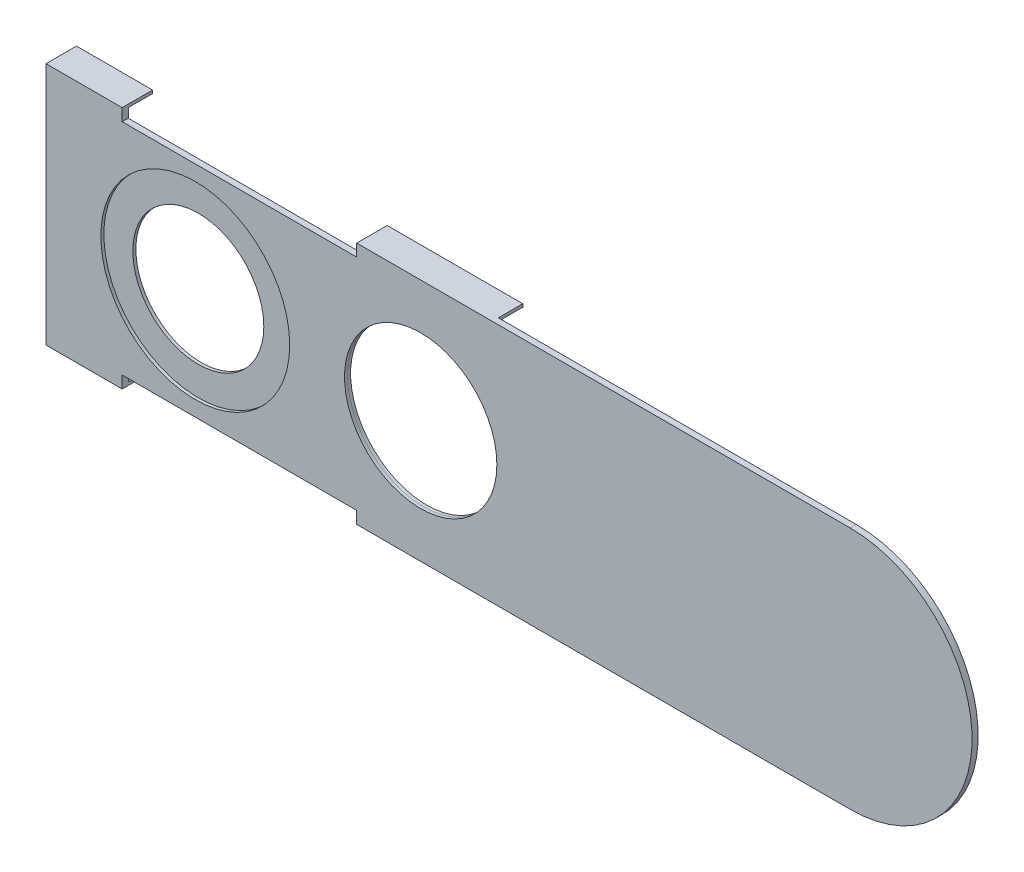
SolidWorks part; units mm, degrees
material "Nickel"
ref_plane "Front Plane" through (0, 0, 0) normal (0, 0, 1) x (1, 0, 0)
ref_plane "Top Plane" through (0, 0, 0) normal (0, 1, 0) x (1, 0, 0)
ref_plane "Right Plane" through (0, 0, 0) normal (1, 0, 0) x (0, 0, -1)
sketch "Sketch1" plane through (0, 0, 0) normal (0, 0, 1) x (1, 0, 0)
  line L0 (0, -10.16) -> (-67.056, -10.16)
  line L1 (-67.056, -10.16) -> (-67.056, 10.16)
  line L2 (-67.056, 10.16) -> (0, 10.16)
  line L3 (10.16, 0) -> (10.16, 15.0411)
  arc A0 (0, -10.16) -> (0, 10.16) centre (0, 0) ccw
  dimension "D1" = 20.32
  dimension "D2" = 77.216
extrude "Boss-Extrude1" add sketch "Sketch1" along normal blind 0.508 contours A0 L2 L1 L0
sketch "Sketch2" plane through (0, 0, 0.508) normal (0, 0, 1) x (1, 0, 0)
  circle A0 centre (-54.61, 0) radius 7.874
  circle A1 centre (-35.814, 0) radius 6.35
  dimension "D2" = 15.748
  dimension "D3" = 12.7
extrude "Cut-Extrude2" cut sketch "Sketch2" against normal blind 0.254
sketch "Sketch5" plane through (0, 0, 0.254) normal (0, 0, 1) x (1, 0, 0)
  circle A0 centre (-35.814, 0) radius 6.3542
extrude "Cut-Extrude3" cut sketch "Sketch5" against normal through all
sketch "Sketch6" plane through (0, 0, 0.254) normal (0, 0, 1) x (1, 0, 0)
  circle A0 centre (-54.61, 0) radius 5.461
  dimension "D1" = 10.922
extrude "Cut-Extrude4" cut sketch "Sketch6" against normal through all
sketch "Sketch7" plane through (0, 0, 0) normal (0, 0, -1) x (-1, 0, 0)
  line L0 (67.056, 10.16) -> (60.706, 10.16)
  line L1 (67.056, 10.16) -> (0, 10.16) construction
  line L2 (60.706, 9.144) -> (60.706, -9.144)
  line L3 (67.056, 10.16) -> (67.056, -10.16) construction
  line L4 (67.056, -10.16) -> (67.056, 10.16) construction
  line L5 (60.706, 10.16) -> (60.706, 9.144)
  line L6 (60.706, -9.144) -> (41.148, -9.144)
  line L7 (60.706, 9.144) -> (41.148, 9.144)
  line L8 (41.148, 9.144) -> (41.148, -9.144)
  line L9 (41.148, 9.144) -> (41.148, 10.16)
  line L10 (41.148, 10.16) -> (60.706, 10.16)
  line L11 (60.706, -9.144) -> (60.706, -10.16)
  line L12 (0, -10.16) -> (67.056, -10.16) construction
  line L13 (60.706, -10.16) -> (41.148, -10.16)
  line L14 (41.148, -10.16) -> (41.148, -9.144)
  point P8 (60.706, 0)
  point P11 (67.056, 0)
  line M9 (0, -10.16) -> (67.056, -10.16)
  line M11 (67.056, 10.16) -> (0, 10.16)
  dimension "D1" = 6.35
  dimension "D2" = 18.288
  dimension "D3" = 19.558
extrude "Cut-Extrude5" cut sketch "Sketch7" against normal through all contours L9 L7 L5 M11 | L14 L11 L6 M9
sketch "Sketch8" plane through (0, 0, 0) normal (0, 0, -1) x (-1, 0, 0)
  line L0 (67.056, -10.16) -> (67.056, 10.16) construction
  line L1 (60.706, 10.16) -> (67.056, 10.16)
  line L2 (60.706, 10.16) -> (60.706, 9.906)
  line L3 (60.706, 9.906) -> (67.056, 9.906)
  line L4 (67.056, 10.16) -> (67.056, 9.906)
  dimension "D1" = 0.254
extrude "Boss-Extrude2" add sketch "Sketch8" along normal blind 2.032
sketch "Sketch10" plane through (0, 0, 0) normal (0, 0, -1) x (-1, 0, 0)
  line L1 (41.148, 10.16) -> (29.8448, 10.16)
  line L2 (41.148, 10.16) -> (41.148, 9.906)
  line L3 (41.148, 9.906) -> (29.8448, 9.906)
  line L4 (29.8448, 10.16) -> (29.8448, 9.906)
  dimension "D1" = 0.254
extrude "Boss-Extrude3" add sketch "Sketch10" along normal blind 2.032
sketch "Sketch11" plane through (0, 0, 0) normal (0, 0, -1) x (-1, 0, 0)
  line L0 (60.706, -9.144) -> (60.706, -10.16) construction
  line L1 (67.056, -10.16) -> (60.706, -10.16)
  line L2 (67.056, -10.16) -> (67.056, -9.906)
  line L3 (67.056, -9.906) -> (60.706, -9.906)
  line L4 (60.706, -10.16) -> (60.706, -9.906)
  dimension "D1" = 0.254
extrude "Boss-Extrude4" add sketch "Sketch11" along normal blind 2.032
sketch "Sketch12" plane through (0, 0, 0) normal (0, 0, -1) x (-1, 0, 0)
  line L1 (41.148, -10.16) -> (29.21, -10.16)
  line L2 (41.148, -10.16) -> (41.148, -9.906)
  line L3 (41.148, -9.906) -> (29.21, -9.906)
  line L4 (29.21, -10.16) -> (29.21, -9.906)
  dimension "D1" = 0.254
  dimension "D2" = 11.938
extrude "Boss-Extrude5" add sketch "Sketch12" along normal blind 2.032
